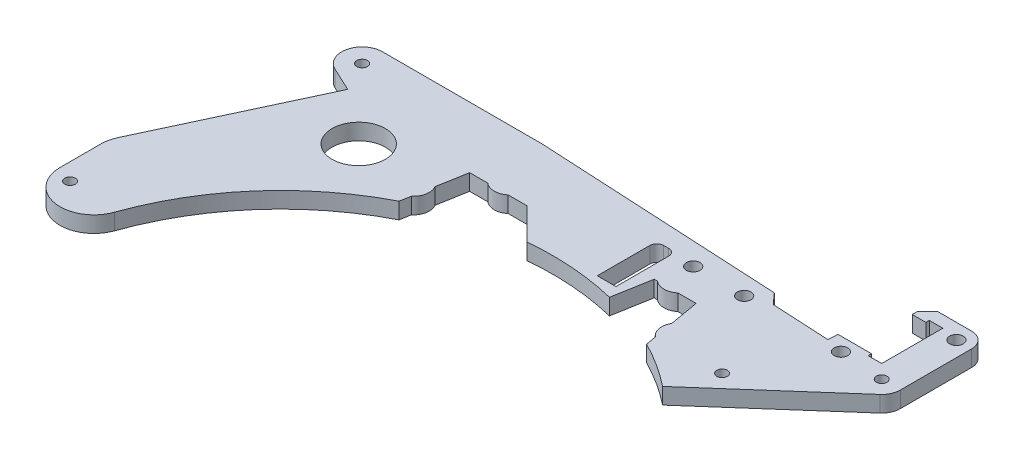
SolidWorks part; units mm, degrees
ref_plane "Front Plane" through (0, 0, 0) normal (0, 0, 1) x (1, 0, 0)
ref_plane "Top Plane" through (0, 0, 0) normal (0, 1, 0) x (1, 0, 0)
ref_plane "Right Plane" through (0, 0, 0) normal (1, 0, 0) x (0, 0, -1)
sketch "Sketch1" plane through (0, 0, 0) normal (0, 1, 0) x (1, 0, 0)
  line L0 (-35.3637, 71.7594) -> (-32.5, 88) construction
  line L1 (-32.5, 88) -> (32.5, 88) construction
  line L2 (32.5, 88) -> (35.3637, 71.7594) construction
  line L3 (0, 0) -> (0, 88) construction
  line L4 (-36.456, 71.323) -> (-35.9081, 74.4307)
  line L5 (-33.3391, 89) -> (-28, 89)
  line L6 (33.3391, 89) -> (34.8662, 80.3396)
  line L7 (-34.8662, 80.3396) -> (-33.3391, 89)
  line L8 (-22, 89) -> (-16.5, 89)
  line L9 (28, 89) -> (33.3391, 89)
  line L10 (35.9081, 74.4307) -> (36.456, 71.323)
  line L11 (-35.9081, 74.4307) -> (-34.8662, 80.3396) construction
  line L12 (-28, 89) -> (-22, 89) construction
  line L13 (22, 89) -> (28, 89) construction
  line L14 (35.9081, 74.4307) -> (34.8662, 80.3396) construction
  line L15 (-94.9589, 30) -> (-94.9589, 42)
  line L16 (68, 122.5) -> (85.5, 122.5)
  line L17 (85.5, 122.5) -> (85.5, 97)
  line L18 (49.5844, 62.9079) -> (83.6335, 92.8711)
  line L19 (-94.022, 46.2262) -> (-72.5378, 92.299)
  line L20 (16.5, 89) -> (7.2694, 79.7694)
  line L21 (-16.5, 89) -> (-7.2694, 79.7694)
  line L22 (16.5, 89) -> (22, 89)
  line L23 (7.2694, 79.7694) -> (0, 72.5) construction
  line L24 (0, 72.5) -> (-7.2694, 79.7694) construction
  line L25 (-77, 107) -> (-30, 107)
  line L26 (-30, 107) -> (42.1611, 103.2182)
  line L27 (61.9767, 99.1756) -> (62.1247, 102)
  line L28 (-72.5378, 92.299) -> (-79.5357, 95.5622)
  line L29 (62.1247, 102) -> (72, 102)
  line L30 (42.1611, 103.2182) -> (45, 100.0653)
  line L31 (61.9767, 99.1756) -> (45, 100.0653)
  line L32 (72, 102) -> (72, 101)
  line L33 (72, 101) -> (76, 101)
  line L34 (76, 101) -> (76, 119)
  line L35 (76, 119) -> (72, 119)
  line L36 (72, 119) -> (72, 118)
  line L37 (72, 118) -> (68, 118)
  line L38 (68, 118) -> (68, 122.5)
  line L39 (80, 97) -> (83.6335, 92.8711) construction
  line L40 (55, 75) -> (58.6335, 70.8711) construction
  circle A0 centre (0, 0) radius 80 construction
  arc A1 (-36.456, 71.323) -> (-75.5295, 26.6704) centre (0, 0) ccw
  arc A2 (-35.9081, 74.4307) -> (-34.8662, 80.3396) centre (-38.8742, 78) ccw
  arc A3 (34.8662, 80.3396) -> (35.9081, 74.4307) centre (38.8742, 78) ccw
  arc A4 (-28, 89) -> (-22, 89) centre (-25, 92.5409) ccw
  arc A5 (22, 89) -> (28, 89) centre (25, 92.5409) ccw
  circle A6 centre (-57, 80) radius 7.85
  arc A7 (49.5844, 62.9079) -> (36.456, 71.323) centre (0, 0) ccw
  circle A8 centre (80, 97) radius 1.5625
  circle A10 centre (67, 110) radius 3.9923 construction
  arc A11 (-7.2694, 79.7694) -> (7.2694, 79.7694) centre (0, 0) cw
  arc A12 (-75.5295, 26.6704) -> (-94.9589, 30) centre (-84.9589, 30) cw
  arc A13 (-94.9589, 42) -> (-94.022, 46.2262) centre (-84.9589, 42) cw
  circle A14 centre (-90, 28) radius 1.5625
  arc A15 (-79.5357, 95.5622) -> (-77, 107) centre (-77, 101) cw
  circle A16 centre (-77, 101) radius 1.5625
  circle A17 centre (81, 118) radius 2
  circle A18 centre (67, 98) radius 2
  arc A19 (83.6335, 92.8711) -> (85.5, 97) centre (80, 97) ccw
  circle A20 centre (55, 75) radius 1.5625
  point P24 (-34.3038, 77.1941)
  dimension "D1" = 160
  dimension "D5" = 160.2
  dimension "D22" = 15.7
  dimension "D25" = 10
  dimension "D29" = 90
  dimension "D37" = 6
  dimension "D47" = 4
  dimension "D51" = 55
  dimension "D12" = 3.125
  dimension "D2" = 88
  dimension "D3" = 65
  dimension "D4" = 80
  dimension "D6" = 1
  dimension "D7" = 1
  dimension "D8" = 0.1
  dimension "D9" = 6
  dimension "D10" = 50
  dimension "D11" = 11
  dimension "D14" = 97
  dimension "D15" = 80
  dimension "D17" = 122.5
  dimension "D18" = 67
  dimension "D19" = 110
  dimension "D20" = 57
  dimension "D21" = 80
  dimension "D23" = 135
  dimension "D24" = 72.5
  dimension "D26" = 30
  dimension "D27" = 12
  dimension "D28" = 65
  dimension "D30" = 28
  dimension "D31" = 3
  dimension "D32" = 107
  dimension "D33" = 30
  dimension "D34" = 3
  dimension "D35" = 22
  dimension "D36" = 45
  dimension "D38" = 77
  dimension "D39" = 17
  dimension "D40" = 8
  dimension "D41" = 8
  dimension "D42" = 5
  dimension "D43" = 1
  dimension "D44" = 4
  dimension "D45" = 4
  dimension "D46" = 85.5
  dimension "D48" = 14
  dimension "D49" = 12
  dimension "D50" = 8
  dimension "D52" = 75
extrude "Boss-Extrude1" add sketch "Sketch1" along normal blind 4.7625
sketch "Sketch2" plane through (0, 4.7625, 0) normal (0, 1, 0) x (1, 0, 0)
  line L0 (19.0265, 77.8075) -> (21, 89)
  line L1 (16.5, 89) -> (22, 89) construction
  line L2 (21, 89) -> (16.5, 89)
  line L3 (16.5, 89) -> (7.2694, 79.7694)
  arc A0 (7.2694, 79.7694) -> (19.0265, 77.8075) centre (0, 0) cw
  arc A1 (7.2694, 79.7694) -> (-7.2694, 79.7694) centre (0, 0) ccw construction
  dimension "D1" = 80
  dimension "D2" = 21
extrude "Boss-Extrude2" add sketch "Sketch2" against normal up to surface (4.7625 mm away) up to face at (67, 0, -96)
sketch "Sketch4" plane through (0, 4.7625, 0) normal (0, 1, 0) x (1, 0, 0)
  line L0 (23.5, 98) -> (38.5, 98) construction
  line L1 (17.25, 81.5) -> (11.75, 81.5)
  line L2 (17.25, 81.5) -> (17.25, 99)
  line L3 (17.25, 99) -> (11.75, 99)
  line L4 (11.75, 81.5) -> (11.75, 99)
  line L5 (14.5, 99) -> (14.5, 81.5) construction
  circle A0 centre (23.5, 98) radius 2
  circle A1 centre (38.5, 98) radius 2
  circle A3 centre (81, 118) radius 2 construction
  dimension "D2" = 15
  dimension "D3" = 98
  dimension "D4" = 23.5
  dimension "D5" = 5.5
  dimension "D6" = 9
  dimension "D7" = 16.5
  dimension "D8" = 1
extrude "Cut-Extrude1" cut sketch "Sketch4" against normal through all
chamfer "Chamfer1" distance 3 angle 45 1 edges at (68, 2.3813, -122.5)
fillet "Fillet1" radius 4.5 1 edges at (85.5, 2.3813, -122.5)
fillet "Fillet2" radius 2 2 edges at (11.75, 2.3813, -99) (17.25, 2.3813, -99)
